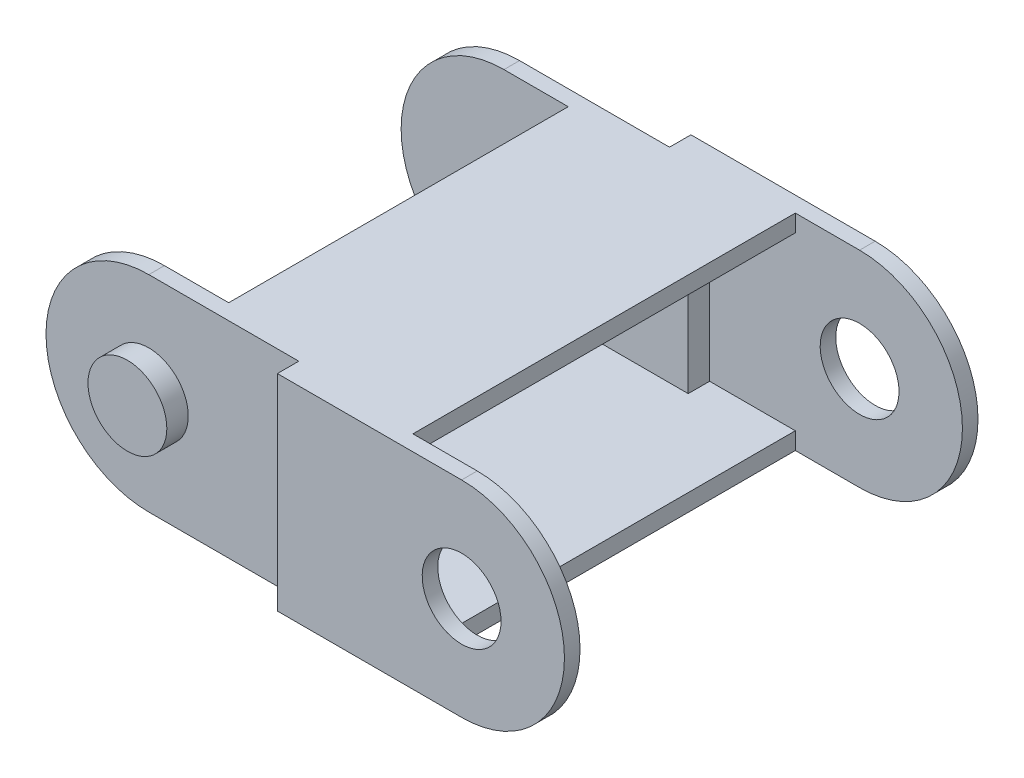
SolidWorks part; units mm, degrees
ref_plane "Front Plane" through (0, 0, 0) normal (0, 0, 1) x (1, 0, 0)
ref_plane "Top Plane" through (0, 0, 0) normal (0, 1, 0) x (1, 0, 0)
ref_plane "Right Plane" through (0, 0, 0) normal (1, 0, 0) x (0, 0, -1)
sketch "Sketch1" plane through (0, 0, 0) normal (0, 0, 1) x (0, 1, 0)
  line L0 (0, 0) -> (0, 19.5) construction
  line L1 (-6, 0) -> (-6, 19.5)
  line L2 (6, 0) -> (6, 19.5)
  arc A0 (-6, 0) -> (6, 0) centre (0, 0) ccw
  arc A1 (6, 19.5) -> (-6, 19.5) centre (0, 19.5) ccw
  circle A2 centre (0, 0) radius 2.3
  point P3 (0, 9.75)
  dimension "D1" = 4.6
  dimension "D3" = 12
  dimension "D2" = 19.5
extrude "Boss-Extrude1" add sketch "Sketch1" along normal mid plane 24.13
sketch "Sketch2" plane through (0, -6, 0) normal (0, -1, 0) x (1, 0, 0)
  line L0 (6, -12.065) -> (6, 12.065) construction
  line L1 (-3.75, 11.156) -> (6, 11.156)
  line L2 (-3.75, 11.156) -> (-3.75, -11.156)
  line L3 (-3.75, -11.156) -> (6, -11.156)
  line L4 (6, 11.156) -> (6, -11.156)
  line L5 (0, 12.065) -> (0, -12.065) construction
  line L6 (-3.75, 11.156) -> (-3.75, 12.065) construction
  line L7 (-19.5, 12.065) -> (0, 12.065) construction
  line L8 (-3.75, -11.156) -> (-3.75, -12.065) construction
  line L9 (-19.5, -12.065) -> (0, -12.065) construction
  line L10 (-25.5, 12.065) -> (-25.5, -12.065) construction
  line L11 (-10.75, 12.065) -> (-25.5, 12.065)
  line L12 (-10.75, 12.065) -> (-10.75, 10.815)
  line L13 (-10.75, 10.815) -> (-25.5, 10.815)
  line L14 (-25.5, 12.065) -> (-25.5, 10.815)
  line L15 (-15.75, 9.906) -> (-15.75, 10.815) construction
  line L16 (-25.5, -10.815) -> (-10.75, -10.815)
  line L17 (-25.5, -10.815) -> (-25.5, -12.065)
  line L18 (-25.5, -12.065) -> (-10.75, -12.065)
  line L19 (-10.75, -10.815) -> (-10.75, -12.065)
  line L20 (-25.5, 9.906) -> (-15.75, 9.906)
  line L21 (-25.5, 9.906) -> (-25.5, -9.906)
  line L22 (-25.5, -9.906) -> (-15.75, -9.906)
  line L23 (-15.75, 9.906) -> (-15.75, -9.906)
  line L24 (-15.75, -9.906) -> (-15.75, -10.815) construction
  point P24 (-10.75, 11.44)
  dimension "D1" = 3.75
  dimension "D3" = 7
  dimension "D4" = 1.25
  dimension "D5" = 19.812
  dimension "D6" = 5
extrude "Cut-Extrude1" cut sketch "Sketch2" against normal through all
sketch "Sketch3" plane through (0, 0, 10.815) normal (0, 0, 1) x (1, 0, 0)
  circle A0 centre (-19.5, 0) radius 2.3
  arc A1 (-19.5, 6) -> (-19.5, -6) centre (-19.5, 0) ccw construction
  circle A2 centre (0, 0) radius 2.3 construction
extrude "Boss-Extrude2" add sketch "Sketch3" along normal up to surface (1.25 mm away) up to face at (-3.875, 0, 12.065)
sketch "Sketch4" plane through (0, 0, -10.815) normal (0, 0, -1) x (1, 0, 0)
  circle A1 centre (-19.5, 0) radius 2.3
  circle A2 centre (-19.5, 0) radius 2.3
  dimension "D1" = 0
extrude "Boss-Extrude3" add sketch "Sketch4" along normal up to surface (1.25 mm away) up to face at (-3.875, 0, -12.065)
sketch "Sketch5" plane through (-3.75, 0, 0) normal (1, 0, 0) x (0, 0, -1)
  line L4 (9.906, 6) -> (9.906, -6) construction
  line L5 (-9.906, 6) -> (-9.906, -6) construction
  line L12 (-9.906, -5) -> (9.906, -5)
  line L13 (9.906, -5) -> (9.906, 5)
  line L14 (9.906, 5) -> (-9.906, 5)
  line L15 (-9.906, 5) -> (-9.906, -5)
  point P8 (-9.906, 0)
  dimension "D1" = 10
extrude "Cut-Extrude2" cut sketch "Sketch5" against normal through all
sketch "Sketch6" plane through (-3.75, 0, 0) normal (1, 0, 0) x (0, 0, -1)
  line L0 (-11.156, 6) -> (-11.156, -6) construction
  line L1 (-9.906, 5) -> (-11.156, 5)
  line L2 (-9.906, 5) -> (-9.906, -5)
  line L3 (-9.906, -5) -> (-11.156, -5)
  line L4 (-11.156, 5) -> (-11.156, -5)
  line L5 (11.156, 6) -> (11.156, -6) construction
  line L6 (9.906, 5) -> (11.156, 5)
  line L7 (9.906, 5) -> (9.906, -5)
  line L8 (9.906, -5) -> (11.156, -5)
  line L9 (11.156, 5) -> (11.156, -5)
  line L10 (-9.906, -5) -> (9.906, -5) construction
extrude "Cut-Extrude3" cut sketch "Sketch6" against normal blind 5
